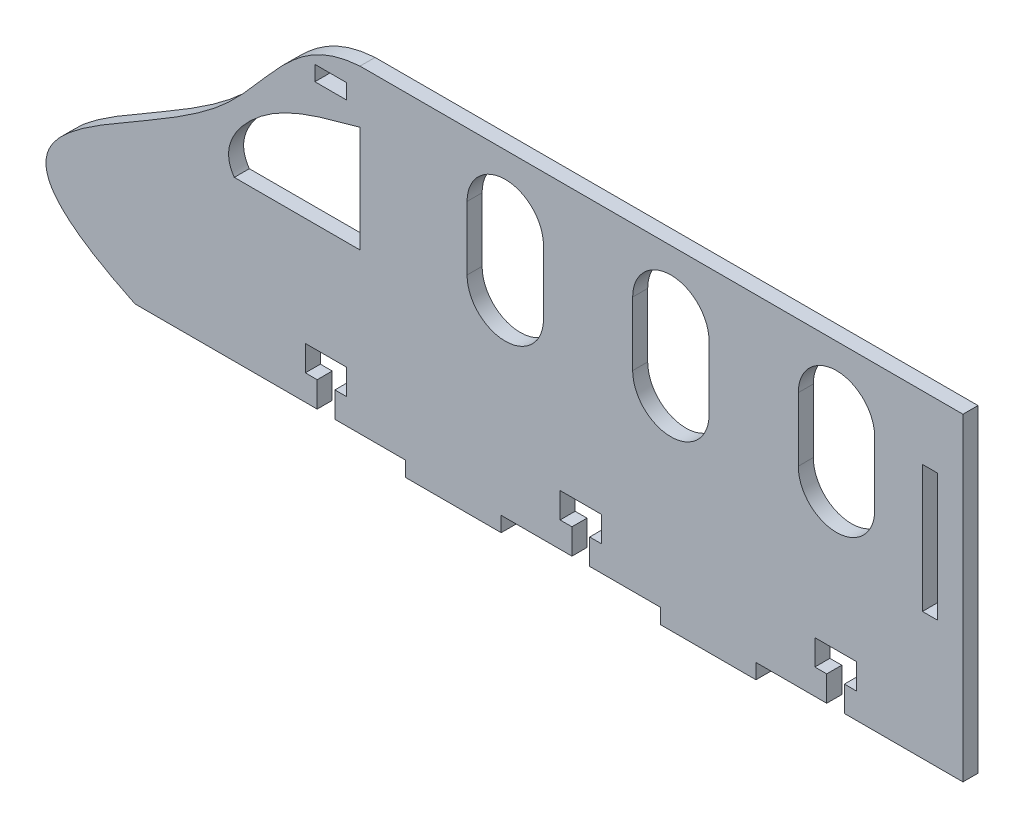
SolidWorks part; units mm, degrees
ref_plane "Front Plane" through (0, 0, 0) normal (0, 0, 1) x (1, 0, 0)
ref_plane "Top Plane" through (0, 0, 0) normal (0, 1, 0) x (1, 0, 0)
ref_plane "Right Plane" through (0, 0, 0) normal (1, 0, 0) x (0, 0, -1)
sketch "Sketch1" plane through (0, 0, 0) normal (0, 0, 1) x (1, 0, 0)
  line L0 (-76.2, -31.75) -> (-76.2, -10.2034) construction
  line L1 (-69.4231, 31.75) -> (50.8, 31.75)
  line L2 (50.8, 31.75) -> (50.8, -31.75)
  line L3 (-114.3, -31.75) -> (-77.9653, -31.75)
  line L4 (25.58, 19.05) -> (25.58, 6.35) construction
  line L5 (-74.4347, -26.67) -> (-72.0725, -26.67)
  line L6 (-29.5275, -21.59) -> (-21.2725, -21.59)
  line L7 (-77.9653, -31.75) -> (-77.9653, -26.67)
  line L8 (-74.4347, -31.75) -> (-60.325, -31.75)
  line L9 (-74.4347, -31.75) -> (-74.4347, -26.67)
  line L10 (-80.3275, -26.67) -> (-77.9653, -26.67)
  line L11 (-80.3275, -26.67) -> (-80.3275, -21.59)
  line L12 (-80.3275, -21.59) -> (-72.0725, -21.59)
  line L13 (-72.0725, -26.67) -> (-72.0725, -21.59)
  line L14 (-21.2725, -26.67) -> (-21.2725, -21.59)
  line L15 (-23.6347, -26.67) -> (-21.2725, -26.67)
  line L16 (-29.5275, -26.67) -> (-27.1653, -26.67)
  line L17 (-27.1653, -31.75) -> (-27.1653, -26.67)
  line L18 (-23.6347, -31.75) -> (-23.6347, -26.67)
  line L19 (-29.5275, -26.67) -> (-29.5275, -21.59)
  line L20 (21.2725, -21.59) -> (29.5275, -21.59)
  line L21 (29.5275, -26.67) -> (29.5275, -21.59)
  line L22 (27.1653, -26.67) -> (29.5275, -26.67)
  line L23 (21.2725, -26.67) -> (23.6347, -26.67)
  line L24 (23.6347, -31.75) -> (23.6347, -26.67)
  line L25 (27.1653, -31.75) -> (27.1653, -26.67)
  line L26 (21.2725, -26.67) -> (21.2725, -21.59)
  line L27 (33.2, 19.05) -> (33.2, 6.35)
  line L28 (17.96, 19.05) -> (17.96, 6.35)
  line L29 (25.58, 12.7) -> (-66.1048, 12.7) construction
  line L30 (-69.4231, 0) -> (-69.4231, 21.1856)
  line L31 (-7.44, 19.05) -> (-7.44, 6.35) construction
  line L32 (0.18, 19.05) -> (0.18, 6.35)
  line L33 (-15.06, 19.05) -> (-15.06, 6.35)
  line L34 (-23.6347, -31.75) -> (-9.525, -31.75)
  line L35 (27.1653, -31.75) -> (50.8, -31.75)
  line L37 (-40.46, 19.05) -> (-40.46, 6.35) construction
  line L38 (-32.84, 19.05) -> (-32.84, 6.35)
  line L39 (-48.08, 19.05) -> (-48.08, 6.35)
  line L40 (45.72, -6.35) -> (42.72, -6.35)
  line L41 (-69.4231, 0) -> (-94.4928, 0)
  line L42 (9.525, -31.75) -> (23.6347, -31.75)
  line L43 (45.72, -6.35) -> (45.72, 19.05)
  line L44 (45.72, 19.05) -> (42.72, 19.05)
  line L45 (-60.325, -31.75) -> (-60.325, -34.75)
  line L46 (-60.325, -34.75) -> (-41.275, -34.75)
  line L47 (-41.275, -31.75) -> (-41.275, -34.75)
  line L48 (-50.8, -31.75) -> (-41.275, -34.75) construction
  line L49 (-60.325, -34.75) -> (-50.8, -31.75) construction
  line L50 (-41.275, -31.75) -> (-27.1653, -31.75)
  line L51 (-9.525, -31.75) -> (-9.525, -34.75)
  line L52 (-9.525, -34.75) -> (9.525, -34.75)
  line L53 (9.525, -31.75) -> (9.525, -34.75)
  line L54 (0, -31.75) -> (9.525, -34.75) construction
  line L55 (-9.525, -34.75) -> (0, -31.75) construction
  line L56 (42.72, -6.35) -> (42.72, 19.05)
  line L57 (-78.4225, 27.553) -> (-72.0725, 27.553)
  line L58 (-78.4225, 27.553) -> (-78.4225, 24.553)
  line L59 (-78.4225, 24.553) -> (-72.0725, 24.553)
  line L60 (-72.0725, 27.553) -> (-72.0725, 24.553)
  line L61 (-78.4225, 27.553) -> (-72.0725, 24.553) construction
  line L62 (-78.4225, 24.553) -> (-72.0725, 27.553) construction
  line L65 (72.0725, -21.59) -> (80.3275, -21.59) [skipped]
  line L66 (80.3275, -26.67) -> (80.3275, -21.59) [skipped]
  line L67 (77.9653, -26.67) -> (80.3275, -26.67) [skipped]
  line L68 (72.0725, -26.67) -> (74.4347, -26.67) [skipped]
  line L69 (74.4347, -31.75) -> (74.4347, -26.67) [skipped]
  line L70 (77.9653, -31.75) -> (77.9653, -26.67) [skipped]
  line L71 (72.0725, -26.67) -> (72.0725, -21.59) [skipped]
  line L72 (-40.46, 12.7) -> (-132.1448, 12.7) construction
  line L73 (-7.44, 12.7) -> (-99.1248, 12.7) construction
  arc A1 (33.2, 19.05) -> (17.96, 19.05) centre (25.58, 19.05) ccw
  arc A2 (17.96, 6.35) -> (33.2, 6.35) centre (25.58, 6.35) ccw
  arc A3 (0.18, 19.05) -> (-15.06, 19.05) centre (-7.44, 19.05) ccw
  arc A4 (-15.06, 6.35) -> (0.18, 6.35) centre (-7.44, 6.35) ccw
  arc A5 (-32.84, 19.05) -> (-48.08, 19.05) centre (-40.46, 19.05) ccw
  arc A6 (-48.08, 6.35) -> (-32.84, 6.35) centre (-40.46, 6.35) ccw
  spline S0 degree 3 poles (-114.3, -31.75) (-155.0752, -12.249) (-95.2038, -1.4861) (-82.9401, 30.9018) (-69.4231, 31.75) knots 0 0 0 0 0.663382 1 1 1 1
  spline S1 degree 3 poles (-69.4231, 21.1856) (-77.0651, 19.0193) (-89.1795, 16.5604) (-97.2927, 3.9521) (-94.4928, 0) knots 0 0 0 0 0.649292 1 1 1 1
  point P3 (25.58, 12.7)
  point P40 (-7.44, 12.7)
  point P49 (-50.8, -31.75)
  point P56 (0, -31.75)
  point P62 (-40.46, 12.7)
  point P74 (-75.2475, 26.053)
  dimension "D14" = 7.62
  dimension "D15" = 12.7
  dimension "D13" = 25.4
  dimension "D22" = 3
  dimension "D2" = 25.4
  dimension "D3" = 165.1
  dimension "D4" = 3
  dimension "D5" = 3
  dimension "D6" = 5.08
  dimension "D7" = 5.08
  dimension "D8" = 3.5306
  dimension "D9" = 1.7653
  dimension "D10" = 8.255
  dimension "D11" = 4.1275
  dimension "D16" = 3
  dimension "D17" = 3
  dimension "D18" = 19.05
  dimension "D19" = 19.05
  dimension "D20" = 5.08
  dimension "D21" = 6.35
  dimension "D12" = 4
extrude "Boss-Extrude1" add sketch "Sketch1" along normal blind 3
